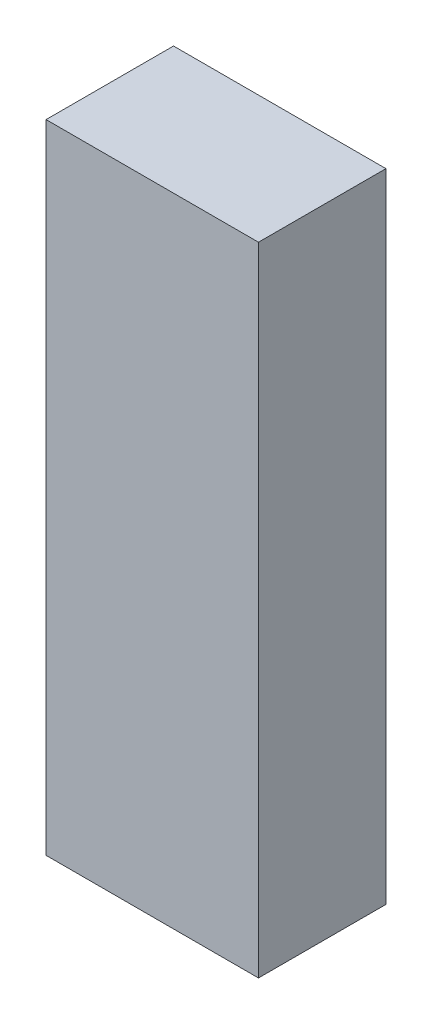
SolidWorks part; units mm, degrees
ref_plane "Plan de face" through (0, 0, 0) normal (0, 0, 1) x (1, 0, 0)
ref_plane "Plan de dessus" through (0, 0, 0) normal (0, 1, 0) x (1, 0, 0)
ref_plane "Plan de droite" through (0, 0, 0) normal (1, 0, 0) x (0, 0, -1)
sketch "Esquisse1" plane through (0, 0, 0) normal (0, 0, 1) x (1, 0, 0)
  line L1 (-23.8024, 36.3772) -> (26.1976, 36.3772)
  line L2 (-23.8024, 36.3772) -> (-23.8024, -113.6228)
  line L3 (-23.8024, -113.6228) -> (26.1976, -113.6228)
  line L4 (26.1976, 36.3772) -> (26.1976, -113.6228)
  dimension "D1" = 150
  dimension "D2" = 50
extrude "Boss.-Extru.1" add sketch "Esquisse1" along normal blind 30
